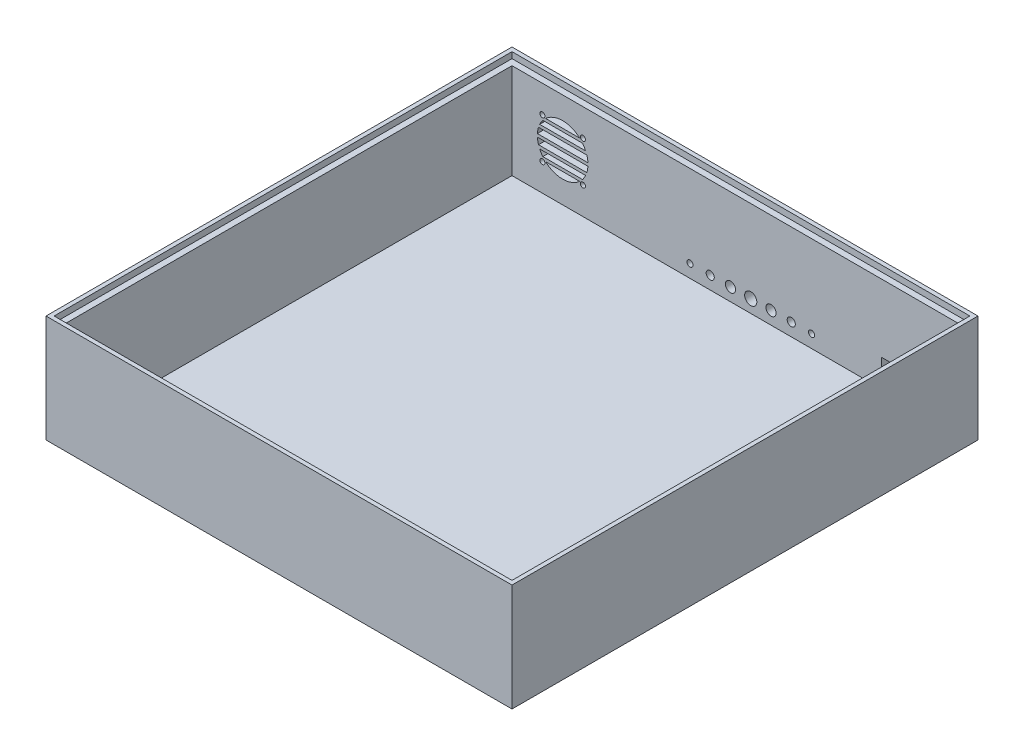
SolidWorks part; units mm, degrees
ref_plane "Plan de face" through (0, 0, 0) normal (0, 0, 1) x (1, 0, 0)
ref_plane "Plan de dessus" through (0, 0, 0) normal (0, 1, 0) x (1, 0, 0)
ref_plane "Plan de droite" through (0, 0, 0) normal (1, 0, 0) x (0, 0, -1)
sketch "Esquisse1" plane through (0, 0, 0) normal (0, 1, 0) x (1, 0, 0)
  line L1 (0, 0) -> (230, 0)
  line L2 (0, 0) -> (0, 230)
  line L3 (0, 230) -> (230, 230)
  line L4 (230, 0) -> (230, 230)
  dimension "D1" = 230
  dimension "D2" = 230
extrude "Boss.-Extru.1" add sketch "Esquisse1" along normal blind 53
sketch "Esquisse2" plane through (0, 53, 0) normal (0, 1, 0) x (1, 0, 0)
  line L0 (230, 230) -> (0, 230) construction
  line L1 (5, 225) -> (225, 225)
  line L2 (5, 225) -> (5, 5)
  line L3 (5, 5) -> (225, 5)
  line L4 (225, 225) -> (225, 5)
  line L5 (0, 230) -> (0, 0) construction
  line L6 (230, 0) -> (230, 230) construction
  line L7 (0, 0) -> (230, 0) construction
  dimension "D1" = 220
  dimension "D2" = 220
  dimension "D3" = 5
  dimension "D4" = 5
  dimension "D5" = 5
  dimension "D6" = 5
extrude "Enlèv. mat.-Extru.1" cut sketch "Esquisse2" against normal blind 50
sketch "Esquisse3" plane through (0, 53, 0) normal (0, 1, 0) x (1, 0, 0)
  line L0 (230, 230) -> (0, 230) construction
  line L1 (2, 228) -> (228, 228)
  line L2 (2, 228) -> (2, 2)
  line L3 (2, 2) -> (228, 2)
  line L4 (228, 228) -> (228, 2)
  line L5 (0, 230) -> (0, 0) construction
  dimension "D1" = 226
  dimension "D2" = 226
  dimension "D3" = 2
  dimension "D4" = 2
extrude "Enlèv. mat.-Extru.2" cut sketch "Esquisse3" against normal blind 3
sketch "Esquisse4" plane through (0, 0, -230) normal (0, 0, -1) x (-1, 0, 0)
  line L0 (0, 53) -> (0, 0) construction
  line L1 (-230, 0) -> (0, 0) construction
  circle A0 centre (-30, 26.5) radius 12.5
  dimension "D1" = 25
  dimension "D2" = 30
  dimension "D3" = 26.5
extrude "Enlèv. mat.-Extru.3" cut sketch "Esquisse4" against normal blind 13
sketch "Esquisse5" plane through (0, 0, -230) normal (0, 0, -1) x (-1, 0, 0)
  line L0 (-230, 0) -> (0, 0) construction
  line L1 (0, 53) -> (0, 0) construction
  circle A0 centre (-40, 36.5) radius 1.25
  circle A1 centre (-20, 36.5) radius 1.25
  circle A2 centre (-20, 16.5) radius 1.25
  circle A3 centre (-40, 16.5) radius 1.25
  dimension "D2" = 2.5
  dimension "D5" = 20
  dimension "D8" = 20
  dimension "D9" = 16.5
  dimension "D11" = 20
extrude "Enlèv. mat.-Extru.4" cut sketch "Esquisse5" against normal blind 13
sketch "Esquisse6" plane through (0, 0, -230) normal (0, 0, -1) x (-1, 0, 0)
  line L1 (-43.1564, 27.25) -> (-16.18, 27.25)
  line L2 (-43.1564, 27.25) -> (-43.1564, 25.75)
  line L3 (-43.1564, 25.75) -> (-16.18, 25.75)
  line L4 (-16.18, 27.25) -> (-16.18, 25.75)
  line L5 (-43.1564, 31.75) -> (-15.8762, 31.75)
  line L6 (-43.1564, 31.75) -> (-43.1564, 30.25)
  line L7 (-43.1564, 30.25) -> (-15.8762, 30.25)
  line L8 (-15.8762, 31.75) -> (-15.8762, 30.25)
  line L9 (-39.8075, 18.75) -> (-20.1925, 18.75)
  line L10 (-38.4076, 17.25) -> (-21.5924, 17.25)
  line L13 (-42.9437, 21.25) -> (-15.6636, 21.25)
  line L14 (-42.9437, 21.25) -> (-42.9437, 22.75)
  line L15 (-42.9437, 22.75) -> (-15.6636, 22.75)
  line L16 (-15.6636, 21.25) -> (-15.6636, 22.75)
  line L21 (-39.8075, 34.25) -> (-20.1925, 34.25)
  line L23 (-21.5924, 35.75) -> (-38.4076, 35.75)
  circle A1 centre (-30, 26.5) radius 12.5 construction
  spline S0 degree 2 poles (-39.8075, 34.25) (-39.5261, 35.4741) (-38.4076, 35.75) knots 0 0 0 1 1 1
  spline S1 degree 2 poles (-21.5924, 35.75) (-20.4769, 35.3497) (-20.1925, 34.25) knots 0 0 0 1 1 1
  spline S2 degree 2 poles (-39.8075, 18.75) (-39.4552, 17.6801) (-38.4076, 17.25) knots 0 0 0 1 1 1
  spline S3 degree 2 poles (-20.1925, 18.75) (-20.3727, 17.5505) (-21.5924, 17.25) knots 0 0 0 1 1 1
  dimension "D1" = 1.5
  dimension "D2" = 9.25
  dimension "D3" = 5.25
  dimension "D4" = 5.25
  dimension "D5" = 9.25
  dimension "D6" = 1.5
extrude "Boss.-Extru.2" add sketch "Esquisse6" against normal blind 5
sketch "Esquisse7" plane through (0, 0, -230) normal (0, 0, -1) x (-1, 0, 0)
  line L0 (-230, 0) -> (0, 0) construction
  line L1 (-230, 53) -> (-230, 0) construction
  circle A0 centre (-215, 8) radius 3
  dimension "D1" = 6
  dimension "D2" = 8
  dimension "D3" = 15
extrude "Enlèv. mat.-Extru.5" cut sketch "Esquisse7" against normal blind 5
sketch "Esquisse9" plane through (0, 0, -230) normal (0, 0, -1) x (-1, 0, 0)
  line L0 (-230, 53) -> (-230, 0) construction
  line L1 (-200, 5.1365) -> (-187.4, 5.1365)
  line L2 (-200, 5.1365) -> (-200, 16.5365)
  line L3 (-200, 16.5365) -> (-187.4, 16.5365)
  line L4 (-187.4, 5.1365) -> (-187.4, 16.5365)
  dimension "D1" = 12.6
  dimension "D2" = 11.4
  dimension "D3" = 30
extrude "Enlèv. mat.-Extru.6" cut sketch "Esquisse9" against normal blind 5
sketch "Esquisse10" plane through (0, 0, -230) normal (0, 0, -1) x (-1, 0, 0)
  circle A0 centre (-152.8317, 9.3599) radius 1.5
  circle A1 centre (-142.8317, 9.3599) radius 2
  circle A2 centre (-132.8317, 9.3599) radius 2.5
  circle A3 centre (-122.8317, 9.3599) radius 3
  circle A4 centre (-112.8317, 9.3599) radius 2.5
  circle A5 centre (-102.8317, 9.3599) radius 2
  circle A6 centre (-92.8317, 9.3599) radius 1.5
  dimension "D1" = 3
  dimension "D2" = 4
  dimension "D3" = 5
  dimension "D4" = 6
  dimension "D11" = 10
extrude "Enlèv. mat.-Extru.7" cut sketch "Esquisse10" against normal blind 10
